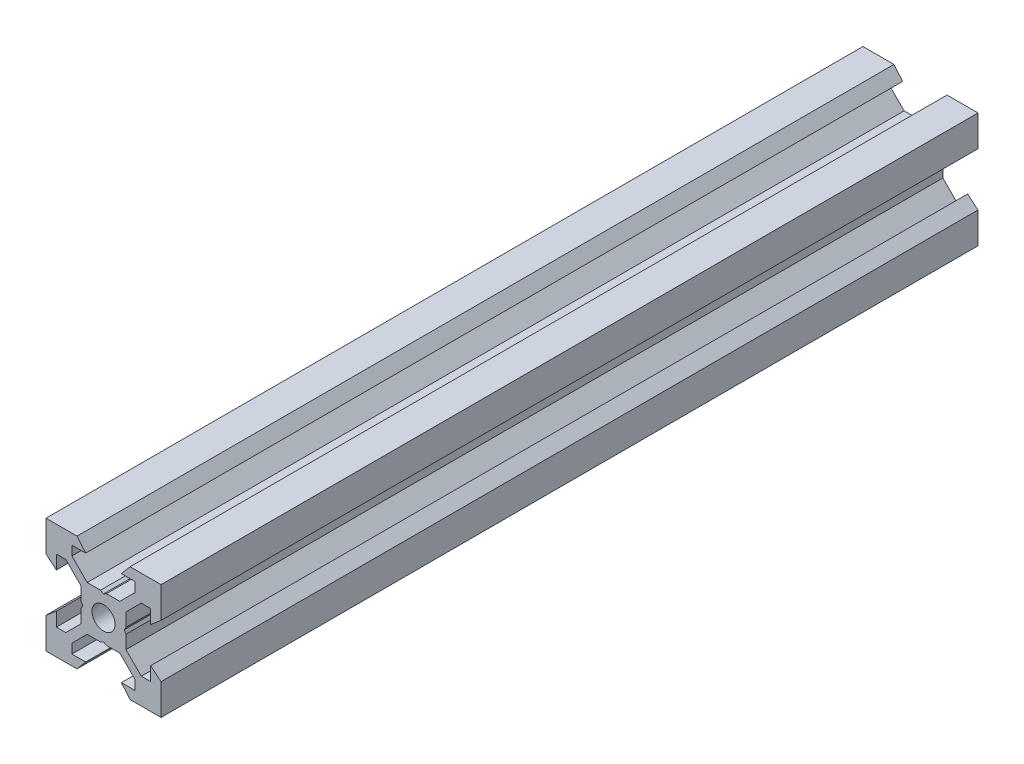
SolidWorks part; units mm, degrees
ref_plane "Front Plane" through (0, 0, 0) normal (0, 0, 1) x (1, 0, 0)
ref_plane "Top Plane" through (0, 0, 0) normal (0, 1, 0) x (1, 0, 0)
ref_plane "Right Plane" through (0, 0, 0) normal (1, 0, 0) x (0, 0, -1)
sketch "Sketch1" plane through (0, 0, 0) normal (0, 0, 1) x (1, 0, 0)
  line L0 (10, 10) -> (4.6104, 10) construction
  line L1 (10, 10) -> (10, 4.6104) construction
  line L2 (10, -10) -> (10, -4.6104) construction
  line L3 (10, -10) -> (4.6104, -10) construction
  line L4 (10, 10) -> (10, 4.6104)
  line L5 (6.5607, 5.5) -> (8.2, 5.5)
  line L6 (5.5, 8.2) -> (5.5, 6.5607)
  line L7 (10, 10) -> (4.6104, 10)
  line L8 (10, 10) -> (10, 4.6104)
  line L9 (6.5607, 5.5) -> (3.9, 2.8393)
  line L10 (5.5, 6.5607) -> (2.8393, 3.9)
  line L11 (10, 4.6104) -> (8.2, 3.1)
  line L12 (4.6104, 10) -> (3.1, 8.2)
  line L13 (8.2, 3.1) -> (8.2, 5.5)
  line L14 (3.1, 8.2) -> (5.5, 8.2)
  line L15 (-6.5607, 5.5) -> (-8.2, 5.5)
  line L16 (6.5607, -5.5) -> (8.2, -5.5)
  line L17 (3.1, -8.2) -> (5.5, -8.2)
  line L18 (8.2, -3.1) -> (8.2, -5.5)
  line L19 (4.6104, -10) -> (3.1, -8.2)
  line L20 (10, -4.6104) -> (8.2, -3.1)
  line L21 (0.5196, -3.9) -> (0, -3.6)
  line L22 (0.5196, 3.9) -> (0, 3.6)
  line L23 (3.6, 0) -> (3.9, -0.5196)
  line L24 (3.9, 0.5196) -> (3.6, 0)
  line L25 (3.9, 0.5196) -> (3.9, 2.8393)
  line L26 (2.8393, 3.9) -> (0.5196, 3.9)
  line L27 (3.9, -2.8393) -> (3.9, -0.5196)
  line L28 (2.8393, -3.9) -> (0.5196, -3.9)
  line L29 (5.5, -6.5607) -> (2.8393, -3.9)
  line L30 (6.5607, -5.5) -> (3.9, -2.8393)
  line L31 (10, -10) -> (10, -4.6104)
  line L32 (10, -10) -> (4.6104, -10)
  line L33 (5.5, -8.2) -> (5.5, -6.5607)
  line L34 (-6.5607, -5.5) -> (-8.2, -5.5)
  line L35 (10, -10) -> (10, -4.6104)
  line L36 (0, 0) -> (0, 8.2) construction
  line L37 (-10, -10) -> (-4.6104, -10) construction
  line L38 (-10, -10) -> (-10, -4.6104) construction
  line L39 (-10, 10) -> (-10, 4.6104) construction
  line L40 (-10, 10) -> (-4.6104, 10) construction
  line L41 (-10, -10) -> (-10, -4.6104)
  line L43 (-5.5, -8.2) -> (-5.5, -6.5607)
  line L44 (-10, -10) -> (-4.6104, -10)
  line L45 (-10, -10) -> (-10, -4.6104)
  line L46 (-6.5607, -5.5) -> (-3.9, -2.8393)
  line L47 (-5.5, -6.5607) -> (-2.8393, -3.9)
  line L48 (-2.8393, -3.9) -> (-0.5196, -3.9)
  line L49 (-3.9, -2.8393) -> (-3.9, -0.5196)
  line L50 (-2.8393, 3.9) -> (-0.5196, 3.9)
  line L51 (-3.9, 0.5196) -> (-3.9, 2.8393)
  line L52 (-3.9, 0.5196) -> (-3.6, 0)
  line L53 (-3.6, 0) -> (-3.9, -0.5196)
  line L54 (-0.5196, 3.9) -> (0, 3.6)
  line L55 (-0.5196, -3.9) -> (0, -3.6)
  line L56 (-10, -4.6104) -> (-8.2, -3.1)
  line L57 (-4.6104, -10) -> (-3.1, -8.2)
  line L58 (-8.2, -3.1) -> (-8.2, -5.5)
  line L59 (-3.1, -8.2) -> (-5.5, -8.2)
  line L60 (-10, -10) -> (10, -10) construction
  line L61 (-10, -10) -> (-10, 10) construction
  line L62 (-3.1, 8.2) -> (-5.5, 8.2)
  line L63 (-8.2, 3.1) -> (-8.2, 5.5)
  line L64 (-4.6104, 10) -> (-3.1, 8.2)
  line L65 (-10, 4.6104) -> (-8.2, 3.1)
  line L66 (-5.5, 6.5607) -> (-2.8393, 3.9)
  line L67 (-6.5607, 5.5) -> (-3.9, 2.8393)
  line L68 (-10, 10) -> (-10, 4.6104)
  line L69 (-10, 10) -> (-4.6104, 10)
  line L70 (-5.5, 8.2) -> (-5.5, 6.5607)
  line L71 (-10, 10) -> (10, 10) construction
  line L72 (-10, 10) -> (-10, 4.6104)
  line L73 (10, -10) -> (10, 10) construction
  line L74 (-10, -10) -> (10, 10) construction
  line L75 (-10, 10) -> (10, -10) construction
  circle A0 centre (0, 0) radius 2
  dimension "D7" = 4
  dimension "D1" = 20
  dimension "D2" = 5.3896
  dimension "D3" = 4.5
  dimension "D4" = 50
  dimension "D5" = 1.8
  dimension "D6" = 1.5104
  dimension "D8" = 5.5
  dimension "D9" = 120
  dimension "D10" = 0.3
  dimension "D11" = 2.3197
  dimension "D12" = 7.8
  dimension "D13" = 7.8
  dimension "D14" = 1.5
  dimension "D15" = 2.6607
extrude "Boss-Extrude1" add sketch "Sketch1" along normal mid plane 142.01 contours L70 L62 L64 L69 L68 L65 L63 L15 L67 L51 L52 L53 L49 L46 L34 L58 L56 L41 L44 L57 L59 L43 L47 L48 L55 L21 L28 L29 L33 L17 L19 L32 L31 L20 L18 L16 L30 L27 L23 L24 L25 L9 L5 L13 L11 L4 L7 L12 L14 L6 L10
